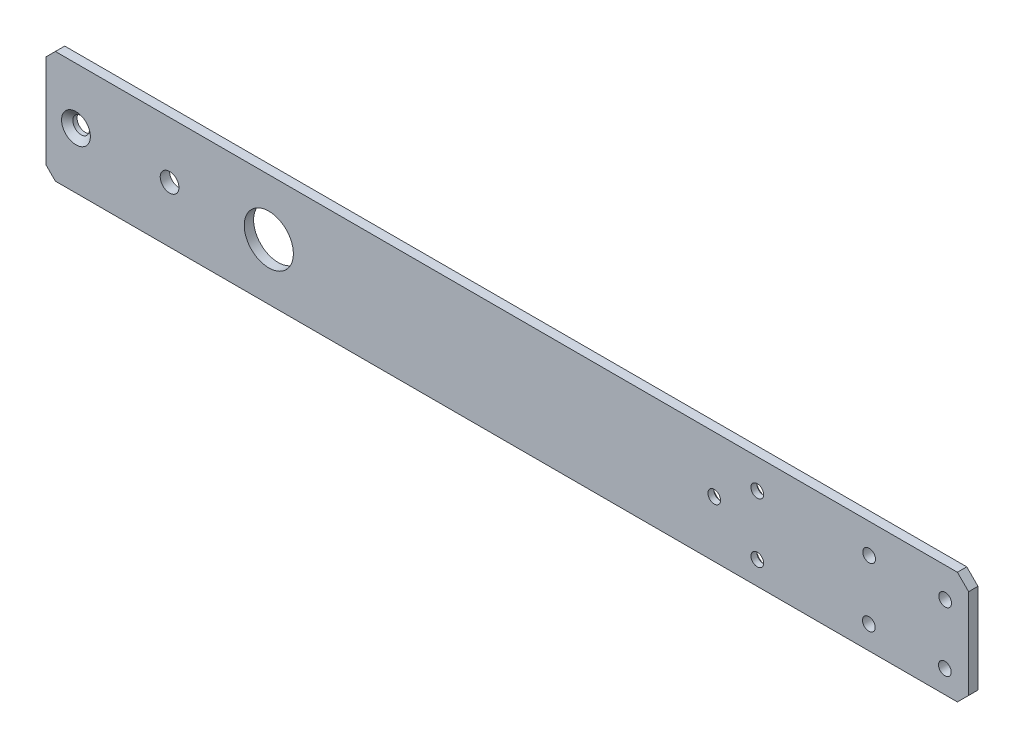
SolidWorks part; units mm, degrees
material "6061-T6 (SS)"
ref_plane "Front Plane" through (0, 0, 0) normal (0, 0, 1) x (1, 0, 0)
ref_plane "Top Plane" through (0, 0, 0) normal (0, 1, 0) x (1, 0, 0)
ref_plane "Right Plane" through (0, 0, 0) normal (1, 0, 0) x (0, 0, -1)
sketch "Sketch1" plane through (0, 0, 0) normal (0, 0, 1) x (1, 0, 0)
  line L0 (0, 19.05) -> (-28.575, 19.05)
  line L1 (0, -19.05) -> (247.2819, -19.05)
  line L2 (0, -19.05) -> (0, 19.05) construction
  line L3 (0, 19.05) -> (254, 19.05)
  line L5 (-28.575, 19.05) -> (-28.575, -19.05)
  line L6 (-28.575, -19.05) -> (0, -19.05)
  line L8 (254, 19.05) -> (247.2819, -19.05)
  circle A1 centre (0, 0) radius 8.3344
  dimension "D3" = 16.6687
  dimension "D1" = 38.1
  dimension "D2" = 254
  dimension "D4" = 80
extrude "Boss-Extrude1" add sketch "Sketch1" along normal mid plane 3.175
hole_wizard "#6 Clearance Hole3" positions "Sketch8" profile "Sketch7" hole size "#6" standard "ANSI Inch" end condition through all
sketch "Sketch8" plane through (0, 0, 1.5875) normal (0, 0, 1) x (1, 0, 0)
  line L9 (159.3222, 8.9914) -> (175.5726, 8.9914) construction
  line L12 (159.3222, -11.1439) -> (172.0222, -11.1439) construction
  line L13 (159.3222, 19.05) -> (159.3222, -19.05) construction
  line L26 (254, 19.05) -> (-28.575, 19.05) construction
  line L28 (-28.575, -19.05) -> (247.2819, -19.05) construction
  line L29 (159.3222, 0) -> (151.0672, 0) construction
  line L30 (165.6722, 8.9914) -> (165.6722, -11.1439) construction
  line L31 (170.6012, -19.2024) -> (177.3462, 19.05) construction
  point P0 (229.3887, 8.9238)
  point P3 (229.2824, -11.3468)
  point P6 (203.5032, -11.1439)
  point P9 (203.6088, 8.9914)
  point P12 (165.6722, 8.9914)
  point P15 (165.6722, -11.1439)
  point P18 (151.0672, 0)
  dimension "D1" = 6.35
  dimension "D2" = 8.255
sketch "Sketch7" plane through (229.3887, 8.9238, 1.5875) normal (1, 0, 0) x (0, -1, 0)
  line L0 (0, 0) -> (0, 3.175)
  line L1 (0, 3.175) -> (2.1526, 3.175)
  line L2 (2.1526, 3.175) -> (2.1526, 0)
  line L5 (2.1526, 0) -> (0, 0)
  line L11 (0, -6.35) -> (0, 107.95) construction
  dimension "Thru Hole Dia." = 4.3053
  dimension "Thru Hole Depth" = 3.175
sketch "Sketch9" plane through (0, 0, 1.5875) normal (0, 0, 1) x (1, 0, 0)
  line L0 (254, 19.05) -> (247.2819, -19.05)
  line L1 (254, 19.05) -> (237.3521, 19.05)
  line L2 (254, 19.05) -> (-28.575, 19.05) construction
  line L3 (237.3521, 19.05) -> (237.3521, -19.05)
  line L4 (-28.575, -19.05) -> (247.2819, -19.05) construction
  line L5 (237.3521, -19.05) -> (247.2819, -19.05)
  line L6 (243.8073, 17.5595) -> (237.0893, -20.5405) construction
extrude "Cut-Extrude1" cut sketch "Sketch9" against normal through all
chamfer "Chamfer1" distance 3.81 angle 45 4 edges at (-28.575, -19.05, 0) (-28.575, 19.05, 0) (237.3521, 19.05, 0) (237.3521, -19.05, 0)
sketch "Sketch10" plane through (0, 0, 1.5875) normal (0, 0, 1) x (1, 0, 0)
  line L0 (-24.765, -19.05) -> (233.5421, -19.05) construction
  line L1 (-24.765, -19.05) -> (-75.565, -19.05)
  line L2 (-24.765, -19.05) -> (-24.765, 19.05)
  line L3 (-24.765, 19.05) -> (-75.565, 19.05)
  line L4 (-75.565, -19.05) -> (-75.565, 19.05)
  dimension "D1" = 50.8
extrude "Boss-Extrude2" add sketch "Sketch10" against normal through all
chamfer "Chamfer2" distance 3.175 angle 45 2 edges at (-75.565, -19.05, 0) (-75.565, 19.05, 0)
hole_wizard "CSK for #10 Flat Head Machine Screw (100)1" positions "Sketch11" profile "Sketch12" countersink size "#10" standard "ANSI Inch" end condition through all
sketch "Sketch11" plane through (0, 0, 1.5875) normal (0, 0, 1) x (1, 0, 0)
  line L0 (0, 0) -> (-75.565, 0) construction
  line L1 (-75.565, 15.875) -> (-75.565, -15.875) construction
  point P0 (-65.405, 0)
  dimension "D1" = 10.16
sketch "Sketch12" plane through (-65.405, 0, 1.5875) normal (1, 0, 0) x (0, -1, 0)
  line L0 (0, 0) -> (0, 3.175)
  line L1 (0, 3.175) -> (2.8067, 3.175)
  line L2 (2.8067, 3.175) -> (2.8067, 1.7477)
  line L3 (2.8067, 1.7477) -> (4.8895, 0)
  line L5 (4.8895, 0) -> (0, 0)
  line L6 (-2.8067, 1.7477) -> (-4.8895, 0) construction
  line L11 (0, -6.35) -> (0, 107.95) construction
  dimension "Thru Hole Dia." = 5.6134
  dimension "Thru Hole Depth" = 3.175
  dimension "Near C'Sink Dia." = 9.779
  dimension "Near C'Sink Angle" = 100
hole_wizard "1/4 (0.25) Diameter Hole1" positions "Sketch13" profile "Sketch14" hole size "1/4" standard "ANSI Inch" end condition through all
sketch "Sketch13" plane through (0, 0, 1.5875) normal (0, 0, 1) x (1, 0, 0)
  line L0 (-75.565, 0) -> (-33.655, 0) construction
  line L1 (-75.565, 15.875) -> (-75.565, -15.875) construction
  circle A0 centre (-65.405, 0) radius 4.8895 construction
  point P0 (-33.655, 0)
  dimension "D1" = 31.75
sketch "Sketch14" plane through (-33.655, 0, 1.5875) normal (1, 0, 0) x (0, -1, 0)
  line L0 (0, 0) -> (0, 3.175)
  line L1 (0, 3.175) -> (3.175, 3.175)
  line L2 (3.175, 3.175) -> (3.175, 0)
  line L5 (3.175, 0) -> (0, 0)
  line L11 (0, -6.35) -> (0, 107.95) construction
  dimension "Thru Hole Dia." = 6.35
  dimension "Thru Hole Depth" = 3.175
hole_wizard "CSK for #6 Flat Head Machine Screw (100)1" positions "Sketch15" profile "Sketch16" countersink size "#6" standard "ANSI Inch" end condition through all
sketch "Sketch15" plane through (0, 0, -1.5875) normal (0, 0, -1) x (-1, 0, 0)
  point P0 (-151.0672, 0)
  point P3 (-165.6722, -11.1439)
  point P6 (-165.6722, 8.9914)
sketch "Sketch16" plane through (151.0672, 0, -1.5875) normal (1, 0, 0) x (0, 1, 0)
  line L0 (0, 0) -> (0, 3.175)
  line L1 (0, 3.175) -> (2.1526, 3.175)
  line L2 (2.1526, 3.175) -> (2.1526, 1.1669)
  line L3 (2.1526, 1.1669) -> (3.5433, 0)
  line L5 (3.5433, 0) -> (0, 0)
  line L6 (-2.1526, 1.1669) -> (-3.5433, 0) construction
  line L11 (0, -6.35) -> (0, 107.95) construction
  dimension "Thru Hole Dia." = 4.3053
  dimension "Thru Hole Depth" = 3.175
  dimension "Near C'Sink Dia." = 7.0866
  dimension "Near C'Sink Angle" = 100
